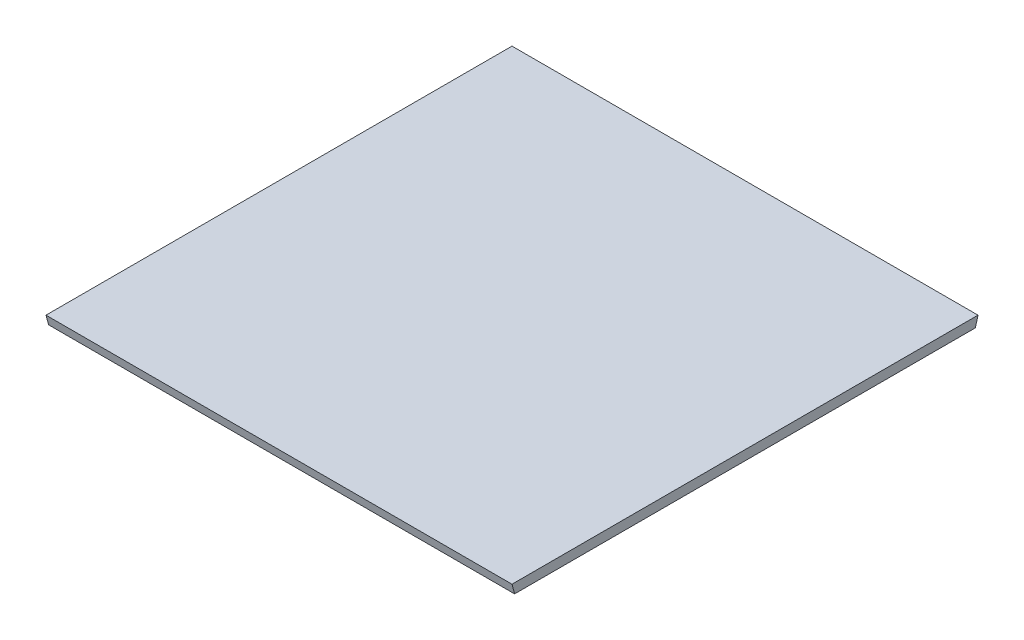
SolidWorks part; units mm, degrees
material "Pine"
ref_plane "Front Plane" through (0, 0, 0) normal (0, 0, 1) x (1, 0, 0)
ref_plane "Top Plane" through (0, 0, 0) normal (0, 1, 0) x (1, 0, 0)
ref_plane "Right Plane" through (0, 0, 0) normal (1, 0, 0) x (0, 0, -1)
sketch "Sketch1" plane through (0, 0, 0) normal (1, 0, 0) x (0, 0, -1)
  line L0 (0, 0) -> (609.6, 0)
  line L1 (609.6, 0) -> (606.197, -12.7)
  line L2 (606.197, -12.7) -> (3.403, -12.7)
  line L3 (3.403, -12.7) -> (0, 0)
  dimension "D1" = 12.7
  dimension "D2" = 609.6
  dimension "D3" = 75
  dimension "D4" = 75
extrude "Boss-Extrude1" add sketch "Sketch1" along normal blind 609.6
ref_plane "Plane1" through (0, 0, -304.8) normal (0, 0, 1) x (1, 0, 0)
equation "\"D1@Sketch1\"=.5in"
equation "\"D2@Sketch1\"=2ft"
equation "\"D4@Sketch1\"=\"D3@Sketch1\""
equation "\"D3@Sketch1\"=(60+90)/2"
